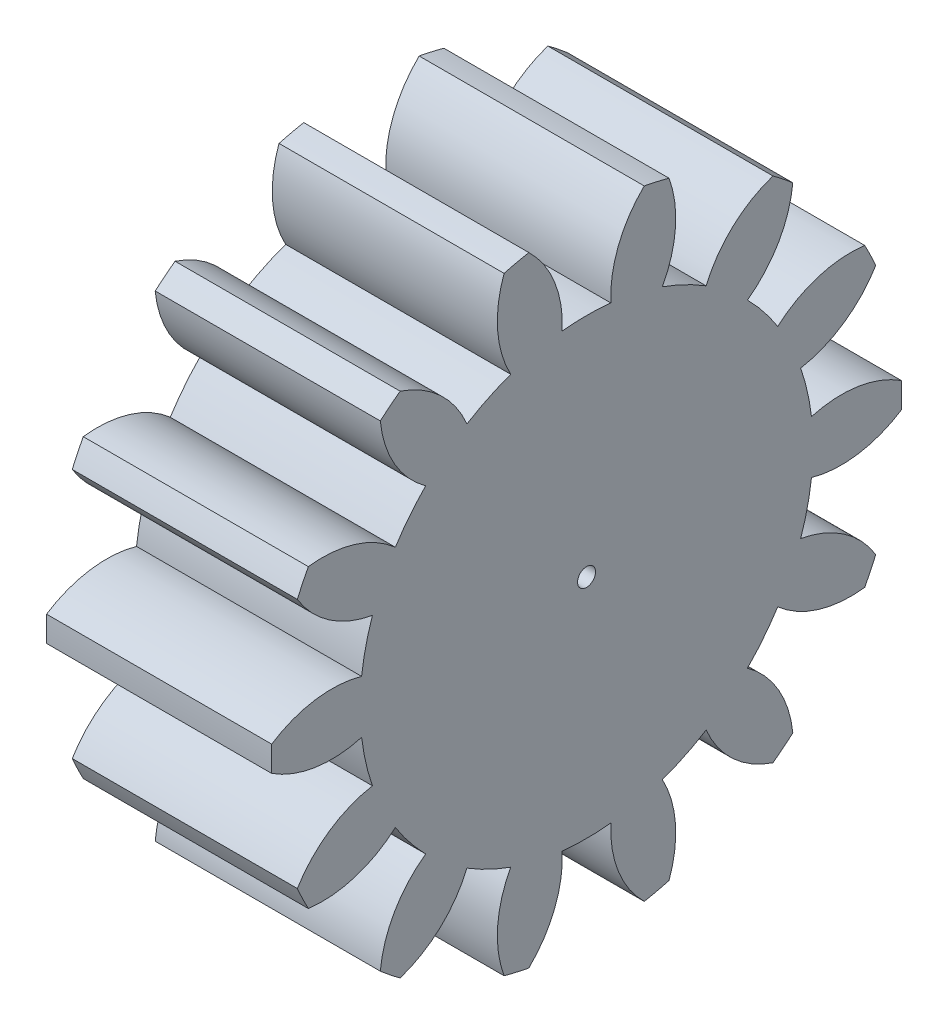
SolidWorks part; units mm, degrees
ref_plane "Plane1" through (0, 0, 0) normal (0, 0, 1) x (1, 0, 0)
ref_plane "Plane2" through (0, 0, 0) normal (0, 1, 0) x (1, 0, 0)
ref_plane "Plane3" through (0, 0, 0) normal (1, 0, 0) x (0, 0, -1)
sketch "HoldingSke" plane through (0, 0, 0) normal (0, 1, 0) x (1, 0, 0)
  line L0 (0, 0) -> (0.5545, -0.1382)
  line L1 (-15, 0) -> (100, 0) construction
  line L2 (0, 0) -> (-2.1039, 2.3779)
  line L3 (0, 0) -> (-11.863, 4.5341)
  line L4 (0, 0) -> (8.3795, 2.0892)
  line L5 (0, 0) -> (-46.8476, -17.4728)
  line L6 (0, 0) -> (-8.2896, -5.593)
  line L7 (-2.1039, 2.3779) -> (8.6586, 51.2059)
  line L8 (-76.2, 54.61) -> (-76.1, 54.61)
  line L9 (-67.7845, 28.3722) -> (-49.3413, 33.142)
  line L10 (-76.2, 71.12) -> (104.1128, 71.12)
  line L11 (0, 0) -> (-10, 0)
  line L12 (-76.2, 101.6) -> (-76.147, 101.6)
  line L13 (24.9733, 27.94) -> (52.9518, 28.4284)
  line L14 (24.9733, 27.94) -> (24.9743, 27.94)
  line L15 (24.9733, 27.94) -> (100.4006, 29.5858)
  line L16 (-63.627, -1.75) -> (-12.827, -1.75)
  circle A0 centre (0, 0) radius 0.4
  circle A1 centre (0, 0) radius 10.0615
  circle A2 centre (0, 0) radius 37.5
  circle A3 centre (0, 0) radius 0.4
  dimension "MHD" = 20.123
  dimension "Hub_dia" = 75
  dimension "Bore" = 0.8
  dimension "MBD" = 0.8
  dimension "Num_teeth" = 14
  dimension "Pitch" = 0.5714
  dimension "Overall_len" = 50
  dimension "Show_teeth" = 14
  dimension "Thickness" = 10
  dimension "OAL" = 50.0001
  dimension "T_dim" = 0.1
  dimension "Ap" = 14.5
  dimension "H" = 19.05
  dimension "Pitch_radius" = 180.3128
  dimension "Width" = 10
  dimension "Backlash" = 0.053
  dimension "Addendum_fac" = 1
  dimension "Dedendum_fac" = 1.25
  dimension "Clearance_fac" = 0.25
  dimension "Dedendum_add" = 0.001
  dimension "Module" = 1.75
sketch "BasProSke" plane through (0, 0, 0) normal (0, 1, 0) x (1, 0, 0)
  line L0 (-10, 0) -> (60, 0) construction
  line L1 (0, 0) -> (0, 14)
  line L2 (0, 0) -> (10, 0)
  line L3 (10, 0) -> (10, 14)
  line L4 (10, 14) -> (0, 14)
  dimension "Thickness" = 10
  dimension "Diameter" = 28
revolve "Base-Revolve" add sketch "BasProSke" angle 360 about L0
sketch "TooCutSke" plane through (0, 0, 0) normal (1, 0, 0) x (0, 0, -1)
  line L1 (0, 0) -> (0, 107) construction
  line L2 (0, 0) -> (-1.4642, 12.1622) construction
  line L3 (0, 0) -> (-5.422, 23.7552) construction
  line L4 (-1.4642, 12.1622) -> (-2.711, 11.8776) construction
  arc A0 (1.0798, 10.0034) -> (-1.0798, 10.0034) centre (0, 0) ccw
  arc A1 (2.5854, 13.785) -> (-2.5854, 13.785) centre (0, 0) ccw
  circle A2 centre (0, 0) radius 12.25 construction
  circle A3 centre (0, 0) radius 11.8598 construction
  arc A4 (-1.0798, 10.0034) -> (-2.5854, 13.785) centre (-5.9738, 10.2454) ccw
  arc A5 (2.5854, 13.785) -> (1.0798, 10.0034) centre (5.9738, 10.2454) ccw
  dimension "Root_dia" = 20.123
  dimension "Overcut_dia" = 28.0508
  dimension "Pitch_dia" = 24.5
  dimension "Base_dia" = 23.7196
  dimension "Flank_rad" = 4.9
  dimension "Half_ang" = 12.857
  dimension "Half_CT" = 1.2788
extrude "ToothCut" cut sketch "TooCutSke" along normal through all
fillet "Breaks" [suppressed] radius 0.035
fillet "RootFillets" [suppressed] radius 0.4385
pattern_circular "TeethCuts" count 14 every 25.714 about axis through (-10, 0, 0) along (1, 0, 0) of "ToothCut", "RootFillets", "Breaks"
sketch "HubNeaOneSke" plane through (0, 0, 0) normal (-1, 0, 0) x (0, 0, 1)
  circle A0 centre (0, 0) radius 10.0615
  dimension "Diameter" = 20.123
extrude "HubNearOne" [suppressed] add sketch "HubNeaOneSke" along normal blind 40.0001
sketch "HubNeaBotSke" plane through (0, 0, 0) normal (-1, 0, 0) x (0, 0, 1)
  circle A0 centre (0, 0) radius 10.0615
  dimension "Diameter" = 20.123
extrude "HubNearBoth" [suppressed] add sketch "HubNeaBotSke" along normal blind 20
ref_plane "FarPln" through (10, 0, 0) normal (1, 0, 0) x (0, 0, -1)
sketch "HubFarSke" plane through (10, 0, 0) normal (1, 0, 0) x (0, 0, -1)
  circle A0 centre (0, 0) radius 10.0615
  dimension "Diameter" = 20.123
extrude "HubFar" [suppressed] add sketch "HubFarSke" along normal blind 20
sketch "BorSke" plane through (0, 0, 0) normal (1, 0, 0) x (0, 0, -1)
  circle A0 centre (0, 0) radius 0.4
  dimension "Diameter" = 0.8
extrude "Bore" cut sketch "BorSke" along normal mid plane 100.0001
sketch "KeySke" plane through (0, 0, 0) normal (1, 0, 0) x (0, 0, -1)
  line L0 (-0.05, 0) -> (-0.05, 0.5)
  line L1 (-0.05, 0.5) -> (0.05, 0.5)
  line L2 (0.05, 0.5) -> (0.05, 0)
  line L3 (0, 0) -> (0, 34) construction
  line L4 (-0.05, 0) -> (0.05, 0)
  dimension "Offset" = 0.5
  dimension "Width" = 0.1
extrude "Keyway" [suppressed] cut sketch "KeySke" along normal mid plane 100.0001
pattern_circular "Keyway2" [suppressed] count 2 every 90 about axis through (-10, 0, 0) along (1, 0, 0)
equation "' \"Module@HoldingSke\" = 6.35"
equation "' \"Num_teeth@HoldingSke\" = 12"
equation "' \"Ap@HoldingSke\" =  20"
equation "' \"Ap@HoldingSke\" = 20"
equation "' \"Width@HoldingSke\" = 0.5 * 25.4"
equation "' \"Hub_dia@HoldingSke\"= 1 * 25.4"
equation "' \"Hub_dia@HoldingSke\" = 1 * 25.4"
equation "' \"Overall_len@HoldingSke\" = 1.0 * 25.4"
equation "' \"Bore@HoldingSke\" = 0.75 * 25.4"
equation "' \"T_dim@HoldingSke\" = 0.1 * 25.4"
equation "' \"Width@KeySke\" = 0.25 * 25.4"
equation "' \"Show_teeth@HoldingSke\" = 13"
equation "' \"Backlash@HoldingSke\" = 0.009 * 25.4"
equation "' \"Addendum_fac@HoldingSke\" = 1.0"
equation "' \"Dedendum_fac@HoldingSke\" = 1.25"
equation "' \"Dedendum_add@HoldingSke\" = 0.00005 * 25.4"
equation "' \"Clearance_fac@HoldingSke\" = 0.25"
equation "\"Pitch@HoldingSke\" = 1 / \"Module@HoldingSke\""
equation "\"Overcut_dia@TooCutSke\" = (\"Num_teeth@HoldingSke\" + 2 * \"Addendum_fac@HoldingSke\") / \"Pitch@HoldingSke\" + 0.002 * 25.4"
equation "\"Pitch_dia@TooCutSke\" = \"Num_teeth@HoldingSke\" / \"Pitch@HoldingSke\""
equation "\"Base_dia@TooCutSke\" = \"Num_teeth@HoldingSke\" / \"Pitch@HoldingSke\" * cos((\"Ap@HoldingSke\"  * 3.14159265 / 180))"
equation "\"Root_dia@TooCutSke\" = (\"Num_teeth@HoldingSke\" + 2) / \"Pitch@HoldingSke\" - 2 * (\"Addendum_fac@HoldingSke\" + \"Dedendum_fac@HoldingSke\") / \"Pitch@HoldingSke\" - \"Dedendum_add@HoldingSke\" * 2"
equation "\"Half_ang@TooCutSke\" = 180 / \"Num_teeth@HoldingSke\""
equation "\"Half_CT@TooCutSke\" = \"Num_teeth@HoldingSke\" / \"Pitch@HoldingSke\" * sin((3.14159265 / 2 / \"Num_teeth@HoldingSke\")) / 2 - 7 * \"Backlash@HoldingSke\" / 4"
equation "\"Flank_rad@TooCutSke\" = \"Num_teeth@HoldingSke\" / \"Pitch@HoldingSke\" / 5"
equation "\"Radius@RootFillets\" = \"Clearance_fac@HoldingSke\" / \"Pitch@HoldingSke\" + \"Dedendum_add@HoldingSke\""
equation "\"Break_rad@Breaks\" = 0.02 / \"Pitch@HoldingSke\""
equation "\"Thickness@HoldingSke\" = \"Width@HoldingSke\""
equation "\"OAL@HoldingSke\" = \"Thickness@HoldingSke\""
equation "\"MHD@HoldingSke\" = (\"Num_teeth@HoldingSke\" + 2) / \"Pitch@HoldingSke\" - 2 * (\"Addendum_fac@HoldingSke\" + \"Dedendum_fac@HoldingSke\")  / \"Pitch@HoldingSke\" - \"Dedendum_add@HoldingSke\" * 2"
equation "\"MBD@HoldingSke\" = (\"Num_teeth@HoldingSke\" + 2) / \"Pitch@HoldingSke\" - 2 * (\"Addendum_fac@HoldingSke\" + \"Dedendum_fac@HoldingSke\")  / \"Pitch@HoldingSke\" - \"Dedendum_add@HoldingSke\" * 2 - 0.002 * 25.4"
equation "\"MHD@HoldingSke\" = ((sgn( \"MHD@HoldingSke\" - \"Hub_dia@HoldingSke\" )-1)*( \"MHD@HoldingSke\" - \"Hub_dia@HoldingSke\" ))/-2+ \"Hub_dia@HoldingSke\""
equation "\"MBD@HoldingSke\" = ((sgn( \"MBD@HoldingSke\" - \"Bore@HoldingSke\" )-1)*( \"MBD@HoldingSke\" - \"Bore@HoldingSke\" ))/-2+ \"Bore@HoldingSke\""
equation "\"OAL@HoldingSke\" = ((sgn( \"OAL@HoldingSke\" - \"Overall_len@HoldingSke\" )+1)*( \"OAL@HoldingSke\" - \"Overall_len@HoldingSke\" ))/2 + \"Overall_len@HoldingSke\" + 0.000002 * 25.4"
equation "\"Num_teeth@TeethCuts\" = int( \"Show_teeth@HoldingSke\" ) + 1"
equation "\"Num_teeth@TeethCuts\" = ((sgn( \"Num_teeth@TeethCuts\" - \"Num_teeth@HoldingSke\" )-1)*( \"Num_teeth@TeethCuts\" - \"Num_teeth@HoldingSke\" ))/-2+ \"Num_teeth@HoldingSke\""
equation "\"Num_teeth@TeethCuts\" = ((sgn( \"Num_teeth@TeethCuts\" - 2.0)+1)*( \"Num_teeth@TeethCuts\" - 2.0))/2 +2.0"
equation "\"Angle@TeethCuts\" = 360.0 / \"Num_teeth@HoldingSke\""
equation "\"Diameter@BasProSke\" = (\"Num_teeth@HoldingSke\" + 2 * \"Addendum_fac@HoldingSke\") / \"Pitch@HoldingSke\""
equation "\"Thickness@BasProSke\"  = \"Thickness@HoldingSke\""
equation "' \"Fillet_rad@BasProSke\" =  \"Thickness@HoldingSke\" * 0.05"
equation "' \"Fillet_rad@BasProSke\" = \"Thickness@HoldingSke\" * 0.05"
equation "\"MHD@HoldingSke\" = ((sgn( \"MHD@HoldingSke\" - \"Root_dia@TooCutSke\" )-1)*( \"MHD@HoldingSke\" - \"Root_dia@TooCutSke\" ))/-2+ \"Root_dia@TooCutSke\""
equation "\"Diameter@HubNeaOneSke\" = \"MHD@HoldingSke\""
equation "\"Length@HubNearOne\" = \"OAL@HoldingSke\" - \"Thickness@BasProSke\""
equation "\"Diameter@HubNeaBotSke\" = \"MHD@HoldingSke\""
equation "\"Length@HubNearBoth\" = ( \"OAL@HoldingSke\" - \"Thickness@BasProSke\" ) / 2.0"
equation "\"Thickness@FarPln\" = \"Thickness@BasProSke\""
equation "\"Diameter@HubFarSke\" = \"MHD@HoldingSke\""
equation "\"Length@HubFar\" = ( \"OAL@HoldingSke\" - \"Thickness@BasProSke\" ) / 2.0"
equation "\"Diameter@BorSke\" = \"MBD@HoldingSke\""
equation "\"D1@Bore\" = \"OAL@HoldingSke\" * 2.0"
equation "\"D1@Keyway\" = \"OAL@HoldingSke\" * 2.0"
equation "\"Offset@KeySke\" = \"T_dim@HoldingSke\" + \"MBD@HoldingSke\" / 2.0"
